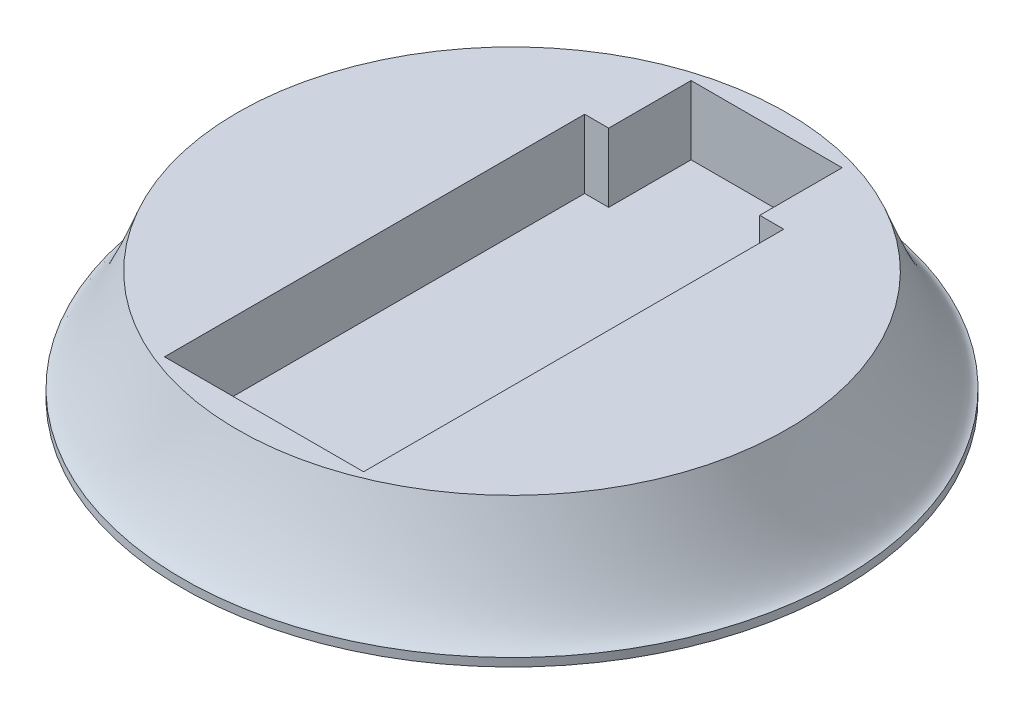
SolidWorks part; units mm, degrees
material "ABS"
ref_plane "Front" through (0, 0, 0) normal (0, 0, 1) x (1, 0, 0)
ref_plane "Top" through (0, 0, 0) normal (0, 1, 0) x (1, 0, 0)
ref_plane "Right" through (0, 0, 0) normal (1, 0, 0) x (0, 0, -1)
sketch "草图1" plane through (0, 0, 0) normal (0, 0, 1) x (1, 0, 0)
  line L0 (0, 0) -> (120, 0)
  line L1 (120, 0) -> (120, 3)
  line L3 (100, 40) -> (0, 40)
  line L4 (0, 40) -> (0, 0)
  spline S0 degree 2 poles (100, 40) (113.4648, 4.3002) (120, 3) knots 0 0 0 0.922508 0.922508 0.922508
  dimension "D1" = 3
  dimension "D2" = 120
  dimension "D3" = 40
  dimension "D4" = 100
revolve "旋转2" add sketch "草图1" angle 360 about L4
sketch "草图2" plane through (0, 40, 0) normal (0, 1, 0) x (1, 0, 0)
  line L0 (0, 113.3126) -> (0, 92.7095) construction
  line L1 (36.25, -90.2905) -> (-36.25, -90.2905)
  line L2 (36.25, -90.2905) -> (36.25, 62.7095)
  line L3 (36.25, 62.7095) -> (27.5, 62.7095)
  line L4 (-36.25, -90.2905) -> (-36.25, 62.7095)
  line L5 (0.4211, -13.7905) -> (-168.5659, -13.7905) construction
  line L6 (-168.5659, -13.7905) -> (162.5682, -13.7905) construction
  line L7 (-27.5, 62.7095) -> (-36.25, 62.7095)
  line L9 (27.5, 62.7095) -> (27.5, 92.7095)
  line L10 (27.5, 92.7095) -> (-27.5, 92.7095)
  line L11 (-27.5, 62.7095) -> (-27.5, 92.7095)
  line L12 (0, 62.7095) -> (0, -150.8993) construction
  dimension "D1" = 72.5
  dimension "D2" = 153
  dimension "D3" = 30
  dimension "D4" = 55
extrude "切除-拉伸1" cut sketch "草图2" against normal blind 25
